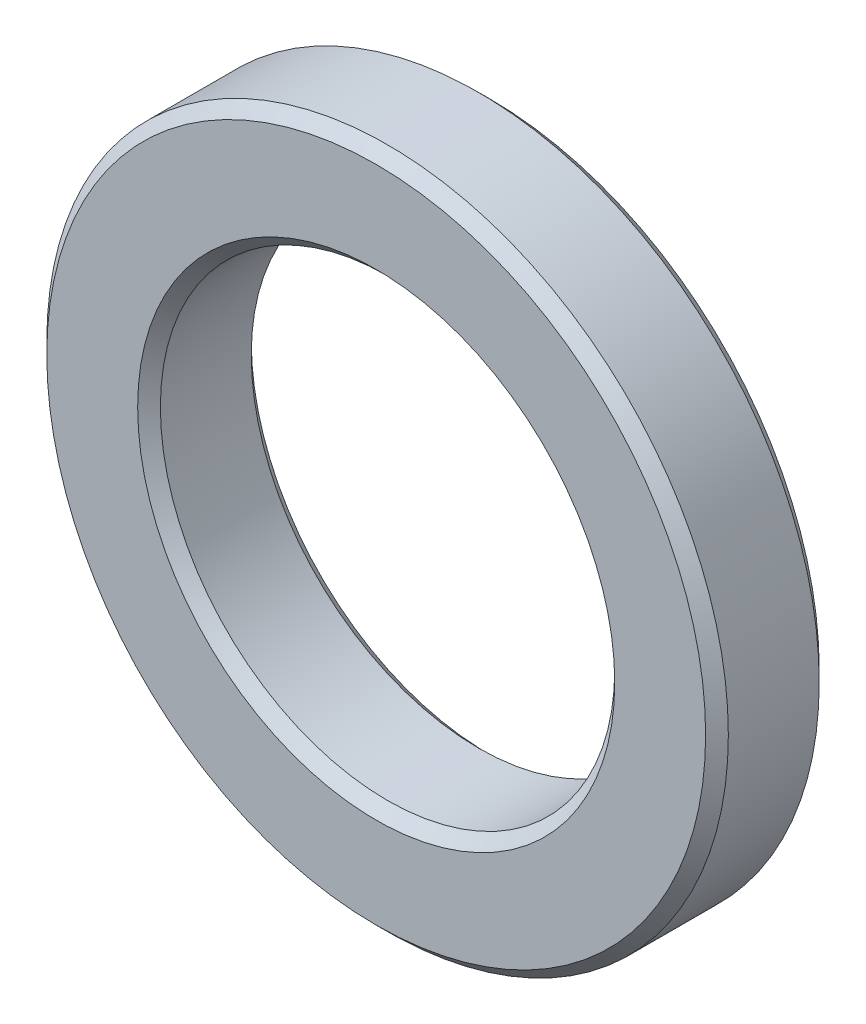
SolidWorks part; units mm, degrees
ref_plane "前视基准面" through (0, 0, 0) normal (0, 0, 1) x (1, 0, 0)
ref_plane "上视基准面" through (0, 0, 0) normal (0, 1, 0) x (1, 0, 0)
ref_plane "右视基准面" through (0, 0, 0) normal (1, 0, 0) x (0, 0, -1)
sketch "草图1" plane through (0, 0, 0) normal (0, 0, 1) x (1, 0, 0)
  circle A0 centre (0, 0) radius 4
  circle A1 centre (0, 0) radius 6
  dimension "D1" = 8
  dimension "D2" = 12
extrude "拉伸1" add sketch "草图1" along normal blind 2
chamfer "倒角1" distance 0.2 angle 45 4 edges at (4, 0, 0) (6, 0, 0) (6, 0, 2) (4, 0, 2)
